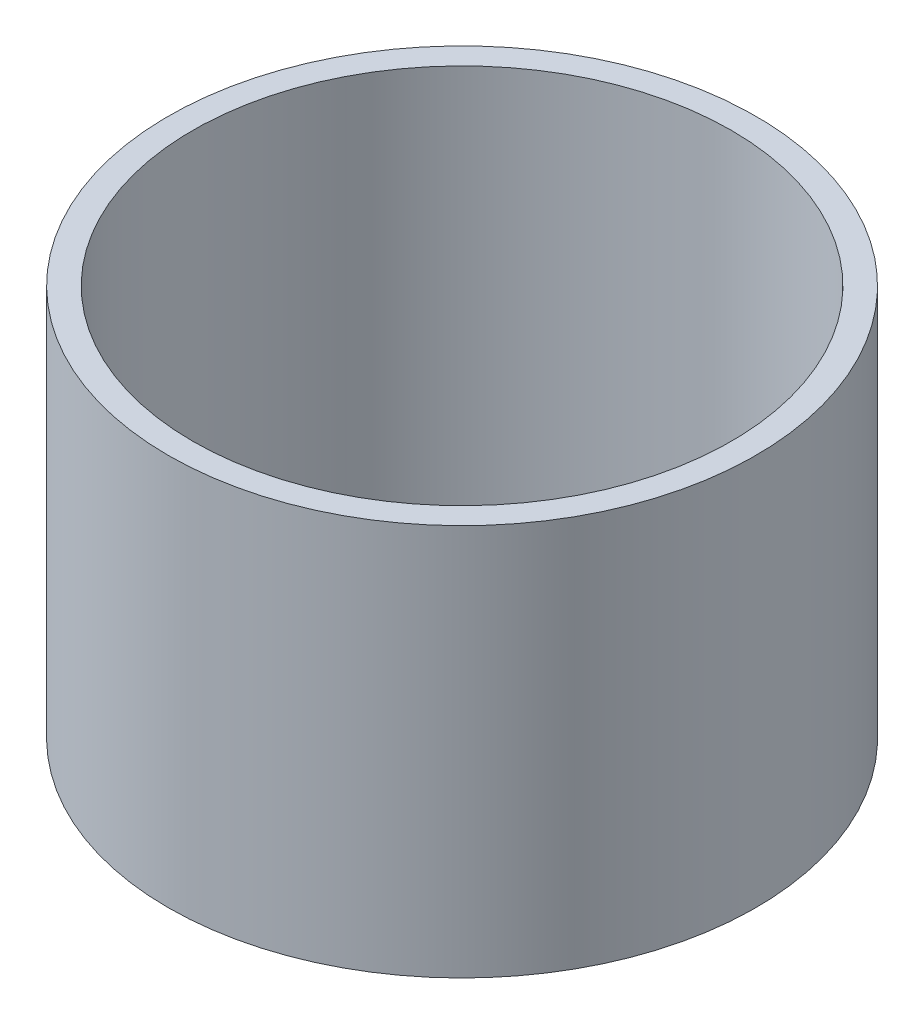
SolidWorks part; units mm, degrees
ref_plane "前基準面" through (0, 0, 0) normal (0, 0, 1) x (1, 0, 0)
ref_plane "上基準面" through (0, 0, 0) normal (0, 1, 0) x (1, 0, 0)
ref_plane "右基準面" through (0, 0, 0) normal (1, 0, 0) x (0, 0, -1)
sketch "草圖1" plane through (0, 0, 0) normal (0, 1, 0) x (1, 0, 0)
  circle A0 centre (0, 0) radius 60
  circle A1 centre (0, 0) radius 55
  dimension "D1" = 120
  dimension "D2" = 110
extrude "填料-伸長1" add sketch "草圖1" along normal blind 80
